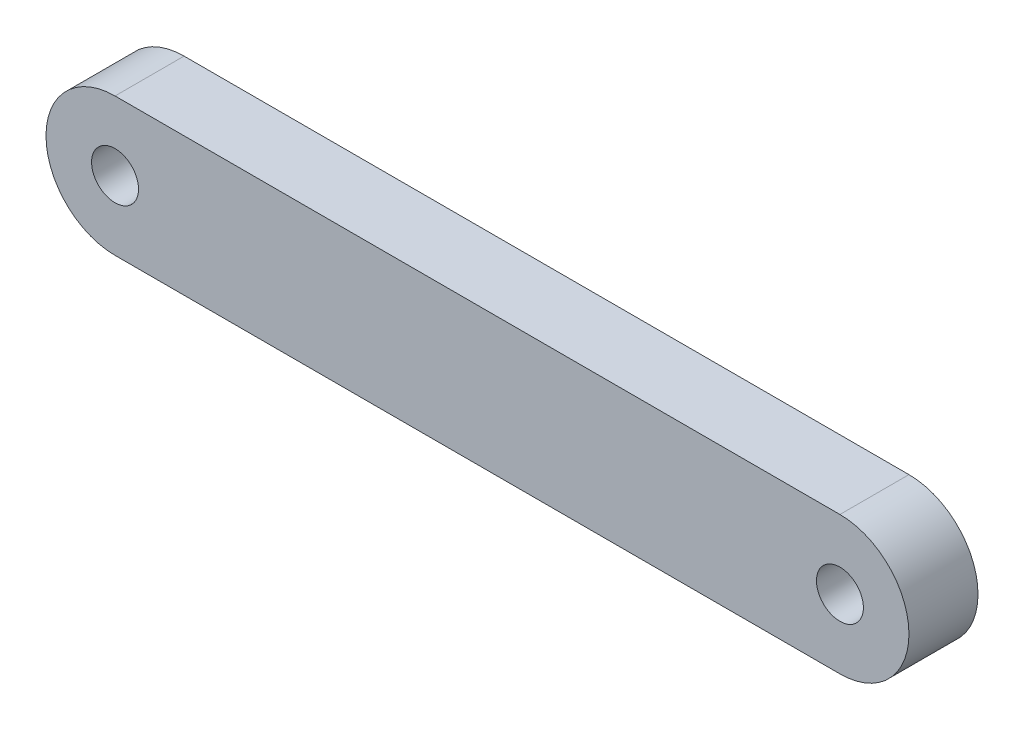
SolidWorks part; units mm, degrees
material "1060 Alloy"
ref_plane "Front" through (0, 0, 0) normal (0, 0, 1) x (1, 0, 0)
ref_plane "Top" through (0, 0, 0) normal (0, 1, 0) x (1, 0, 0)
ref_plane "Right" through (0, 0, 0) normal (1, 0, 0) x (0, 0, -1)
sketch "Sketch1" plane through (0, 0, 0) normal (0, 0, 1) x (1, 0, 0)
  line L0 (0, 0) -> (66.675, 0) construction
  line L2 (0, 6.35) -> (66.675, 6.35)
  line L3 (0, -6.35) -> (66.675, -6.35)
  arc A0 (0, 6.35) -> (0, -6.35) centre (0, 0) ccw
  arc A1 (66.675, -6.35) -> (66.675, 6.35) centre (66.675, 0) ccw
  circle A2 centre (0, 0) radius 2.159
  circle A3 centre (66.675, 0) radius 2.159
  point P5 (33.3375, 0)
  dimension "D1" = 4.318
  dimension "D2" = 66.675
  dimension "D3" = 6.35
extrude "Boss-Extrude1" add sketch "Sketch1" along normal blind 6.35
